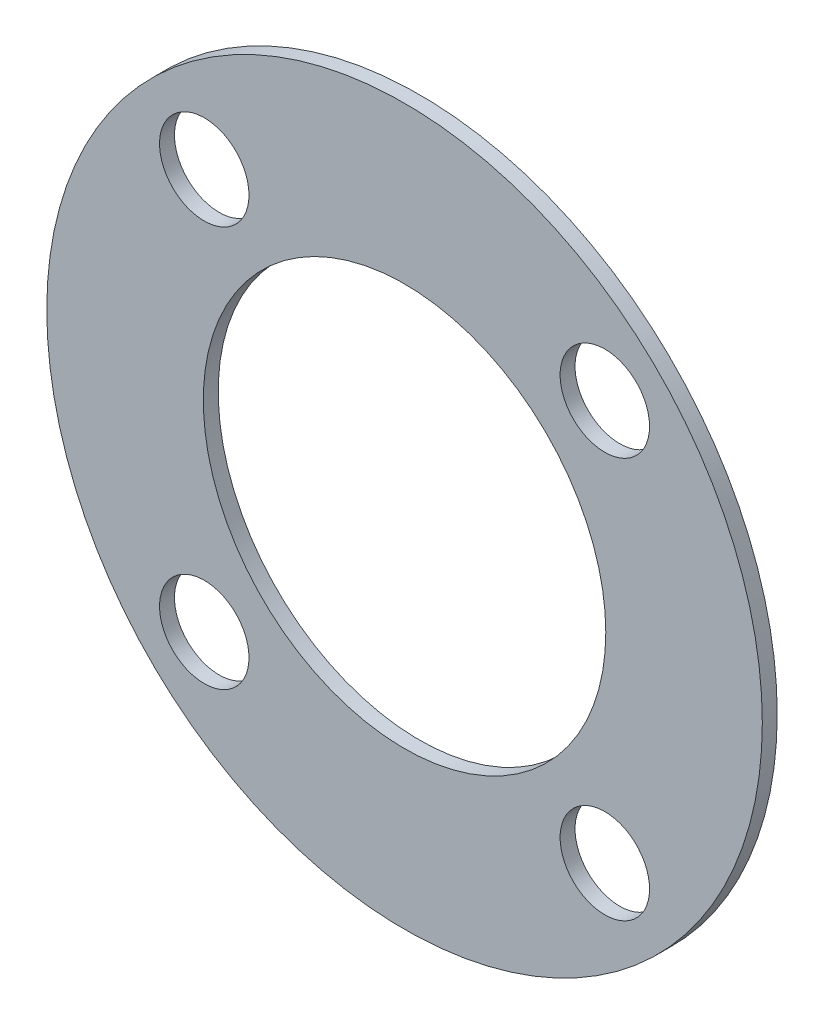
SolidWorks part; units mm, degrees
material "VITON"
ref_plane "Front Plane" through (0, 0, 0) normal (0, 0, 1) x (1, 0, 0)
ref_plane "Top Plane" through (0, 0, 0) normal (0, 1, 0) x (1, 0, 0)
ref_plane "Right Plane" through (0, 0, 0) normal (1, 0, 0) x (0, 0, -1)
sketch "Sketch1" plane through (0, 0, 0) normal (0, 0, 1) x (1, 0, 0)
  circle A0 centre (0, -201.6125) radius 42.8625 construction
  circle A2 centre (42.6562, -244.2687) radius 9.525 construction
  circle A3 centre (-42.6562, -244.2687) radius 9.525 construction
  circle A4 centre (-42.6562, -158.9563) radius 9.525 construction
  circle A5 centre (0, -201.6125) radius 76.2 construction
  circle A6 centre (0, -201.6125) radius 42.8625
  circle A7 centre (42.6562, -158.9563) radius 9.525 construction
  circle A8 centre (42.6562, -244.2687) radius 9.525
  circle A9 centre (-42.6562, -244.2687) radius 9.525
  circle A10 centre (-42.6562, -158.9563) radius 9.525
  circle A11 centre (0, -201.6125) radius 76.2
  circle A12 centre (42.6562, -158.9563) radius 9.525
extrude "Extrude1" add sketch "Sketch1" along normal blind 3.175
